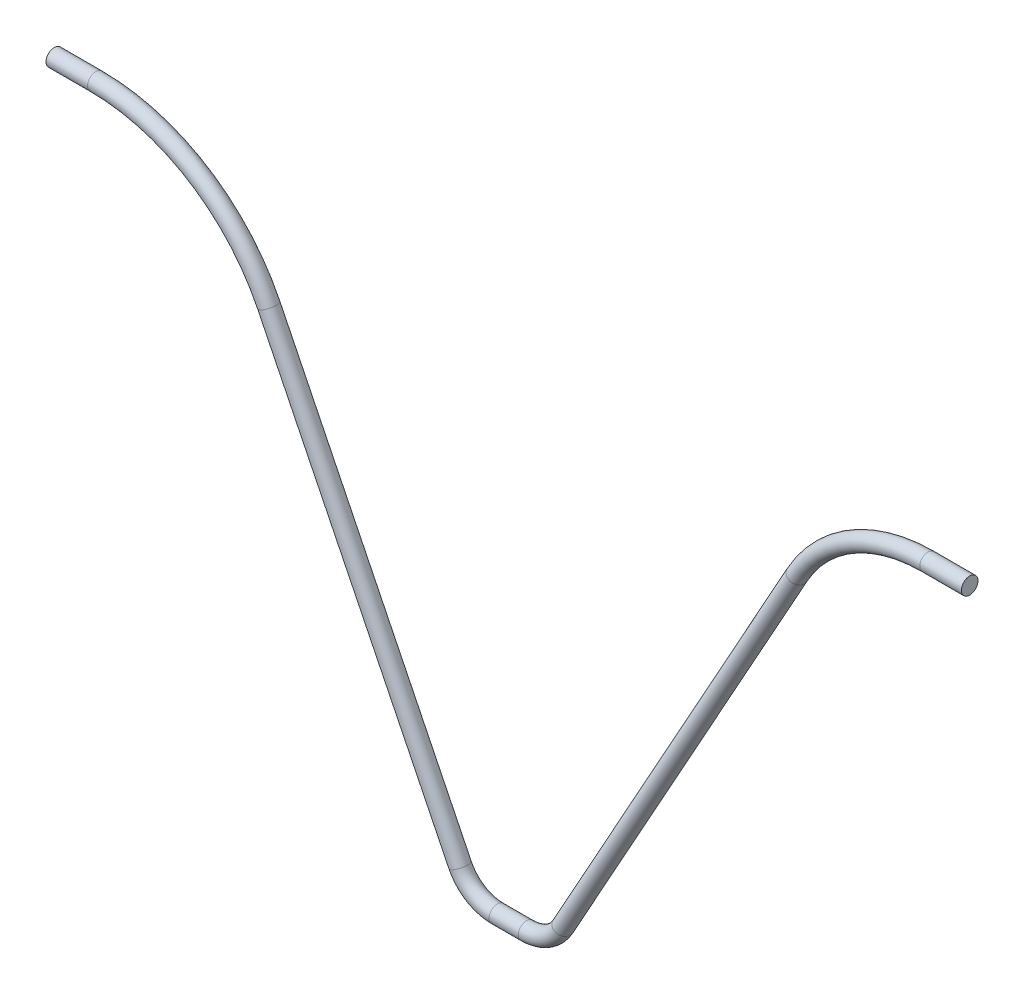
SolidWorks part; units mm, degrees
ref_plane "Front Plane" through (0, 0, 0) normal (0, 0, 1) x (1, 0, 0)
ref_plane "Top Plane" through (0, 0, 0) normal (0, 1, 0) x (1, 0, 0)
ref_plane "Right Plane" through (0, 0, 0) normal (1, 0, 0) x (0, 0, -1)
sketch "Sketch1" plane through (0, 0, 0) normal (0, 0, 1) x (1, 0, 0)
  line L0 (-110, 81) -> (-100, 81)
  line L1 (-58.4474, 55.123) -> (-12.4745, -38.4111)
  line L2 (-3.5, -44) -> (3.5, -44)
  line L3 (12.2423, -38.855) -> (68.5128, 62.4695)
  line L4 (100, 81) -> (110, 81)
  arc A0 (-100, 81) -> (-58.4474, 55.123) centre (-100, 34.6995) cw
  arc A1 (-12.4745, -38.4111) -> (-3.5, -44) centre (-3.5, -34) ccw
  arc A2 (3.5, -44) -> (12.2423, -38.855) centre (3.5, -34) ccw
  arc A3 (68.5128, 62.4695) -> (100, 81) centre (100, 44.9831) cw
  point P13 (0, -44)
  dimension "D7" = 10
  dimension "D8" = 10
  dimension "D1" = 10
  dimension "D2" = 10
  dimension "D3" = 125
  dimension "D4" = 125
  dimension "D5" = 7
  dimension "D6" = 0
  dimension "D9" = 100
  dimension "D10" = 100
sweep "Sweep1" add path "Sketch1" circular profile diameter 4 parameters "D3"=4
